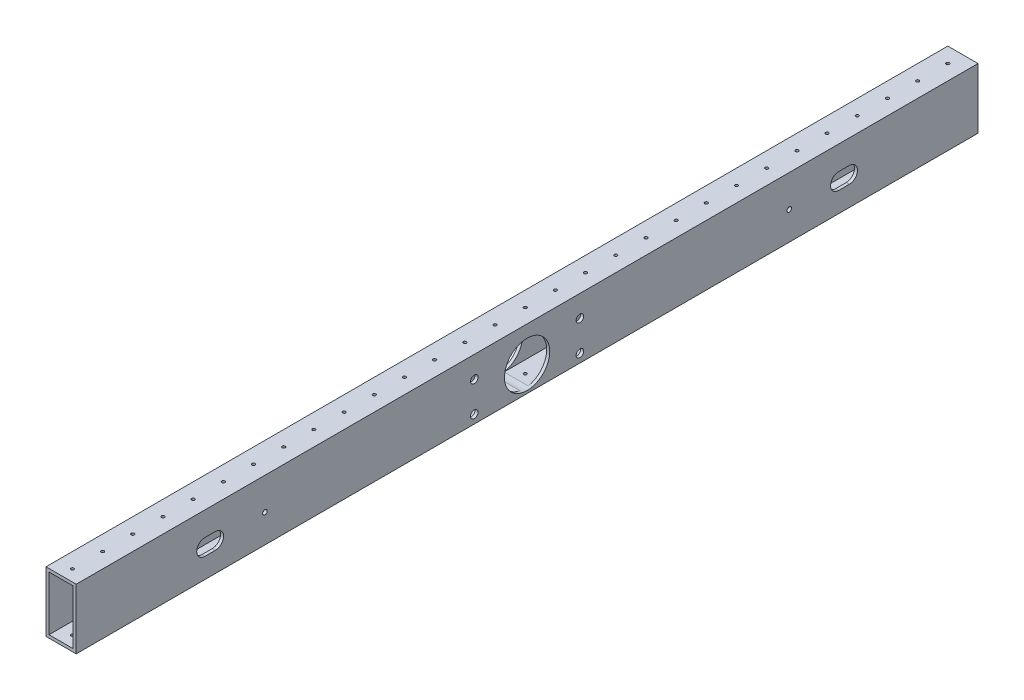
SolidWorks part; units mm, degrees
ref_plane "Front Plane" through (0, 0, 0) normal (0, 0, 1) x (1, 0, 0)
ref_plane "Top Plane" through (0, 0, 0) normal (0, 1, 0) x (1, 0, 0)
ref_plane "Right Plane" through (0, 0, 0) normal (1, 0, 0) x (0, 0, -1)
sketch "Sketch1" plane through (0, 0, 0) normal (0, 0, 1) x (1, 0, 0)
  line L1 (-12.7, -25.4) -> (12.7, -25.4)
  line L2 (-12.7, -25.4) -> (-12.7, 25.4)
  line L3 (-12.7, 25.4) -> (12.7, 25.4)
  line L4 (12.7, -25.4) -> (12.7, 25.4)
  point P5 (-12.7, 0)
  point P7 (0, 25.4)
  dimension "D1" = 50.8
  dimension "D2" = 25.4
extrude "Extrude-Thin1" add sketch "Sketch1" along normal mid plane 758.825 thin thin type one direction reverse wall 2.54
sketch "Sketch2" plane through (0, 25.4, 0) normal (0, 1, 0) x (1, 0, 0)
  line L0 (12.7, 379.4125) -> (-12.7, 379.4125) construction
  circle A0 centre (0, 366.7125) radius 1.27
  point P5 (0, 379.4125)
  dimension "D1" = 2.54
  dimension "D2" = 12.7
extrude "Cut-Extrude1" cut sketch "Sketch2" against normal through all
pattern_linear "LPattern1" count 30 spacing 25.4 along (0, 0, 1) of "Cut-Extrude1"
sketch "Sketch4" plane through (-12.7, 0, 0) normal (-1, 0, 0) x (0, 0, 1)
  line L0 (0, -4.1275) -> (266.6879, -1.5875) construction
  line L1 (0, -4.1275) -> (-266.6879, -1.5875) construction
  line L3 (-262.2429, -1.5875) -> (-220.5869, -1.5875) construction
  line L4 (0, 25.4) -> (0, -25.4) construction
  line L5 (379.4125, 25.4) -> (-379.4125, 25.4) construction
  line L6 (379.4125, -25.4) -> (-379.4125, -25.4) construction
  line L9 (-262.2429, -1.5875) -> (-271.1329, -1.5875) construction
  line L10 (-262.2429, 5.2705) -> (-271.1329, 5.2705)
  line L11 (-262.2429, -8.4455) -> (-271.1329, -8.4455)
  line L12 (262.2429, -1.5875) -> (271.1329, -1.5875) construction
  line L13 (262.2429, 5.2705) -> (271.1329, 5.2705)
  line L14 (262.2429, -8.4455) -> (271.1329, -8.4455)
  circle A0 centre (0, -4.1275) radius 101.6 construction
  circle A1 centre (266.6879, -1.5875) radius 101.6 construction
  circle A2 centre (-266.6879, -1.5875) radius 101.6 construction
  circle A3 centre (0, -4.1275) radius 19.05
  arc A6 (-262.2429, 5.2705) -> (-262.2429, -8.4455) centre (-262.2429, -1.5875) cw
  arc A7 (-271.1329, -8.4455) -> (-271.1329, 5.2705) centre (-271.1329, -1.5875) cw
  circle A8 centre (-220.5869, -1.5875) radius 1.9304
  arc A9 (262.2429, 5.2705) -> (262.2429, -8.4455) centre (262.2429, -1.5875) ccw
  arc A10 (271.1329, -8.4455) -> (271.1329, 5.2705) centre (271.1329, -1.5875) ccw
  circle A11 centre (220.5869, -1.5875) radius 1.9304
  point P9 (-368.2879, -1.5875)
  point P22 (266.6879, -1.5875)
  point P27 (-266.6879, -1.5875)
  dimension "D1" = 203.2
  dimension "D4" = 38.1
  dimension "D5" = 6.858
  dimension "D7" = 41.656
  dimension "D6" = 3.8608
  dimension "D2" = 26.9875
  dimension "D3" = 266.7
  dimension "D8" = 8.89
  dimension "D9" = 4.1275
extrude "Cut-Extrude2" cut sketch "Sketch4" against normal through all
sketch "Sketch5" plane through (-12.7, 0, 0) normal (-1, 0, 0) x (0, 0, 1)
  circle A8 centre (-44.45, 7.18) radius 3.175 construction
  circle A9 centre (-44.45, -18.22) radius 3.175 construction
  circle A10 centre (44.45, 7.18) radius 3.175 construction
  circle A11 centre (44.45, -18.22) radius 3.175 construction
  circle A12 centre (-44.45, 7.18) radius 3.175
  circle A13 centre (-44.45, -18.22) radius 3.175
  circle A14 centre (44.45, 7.18) radius 3.175
  circle A15 centre (44.45, -18.22) radius 3.175
extrude "Cut-Extrude3" cut sketch "Sketch5" against normal through all
